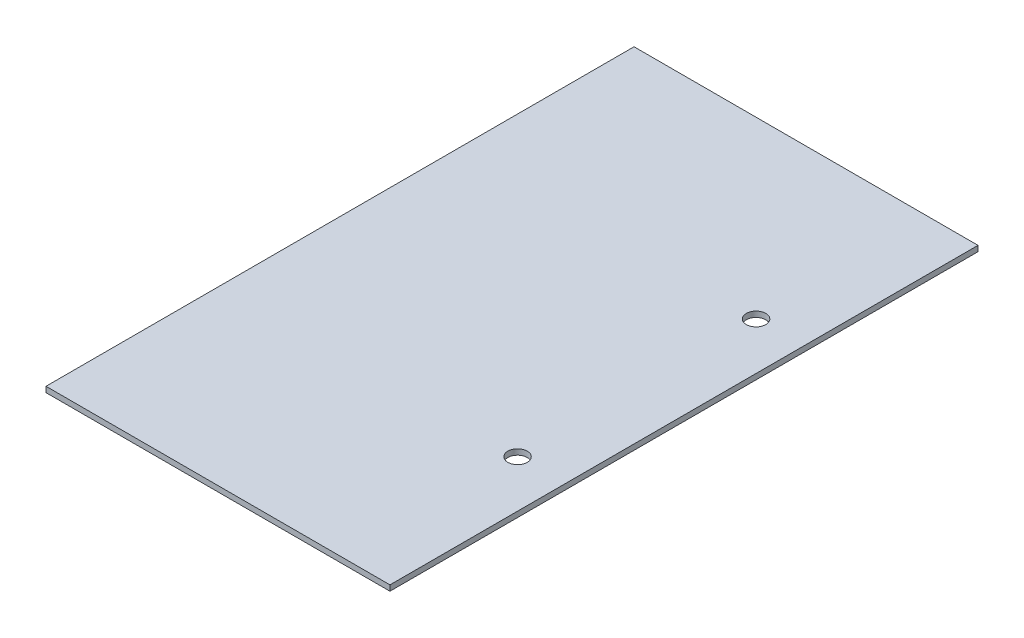
SolidWorks part; units mm, degrees
ref_plane "Front Plane" through (0, 0, 0) normal (0, 0, 1) x (1, 0, 0)
ref_plane "Top Plane" through (0, 0, 0) normal (0, 1, 0) x (1, 0, 0)
ref_plane "Right Plane" through (0, 0, 0) normal (1, 0, 0) x (0, 0, -1)
sketch "Sketch1" plane through (0, 0, 0) normal (0, 1, 0) x (1, 0, 0)
  line L0 (31, 0) -> (22.5, 0) construction
  line L1 (-31, 53) -> (31, 53)
  line L2 (-31, 53) -> (-31, -53)
  line L3 (-31, -53) -> (31, -53)
  line L4 (31, 53) -> (31, -53)
  line L5 (-31, 53) -> (31, -53) construction
  line L6 (-31, -53) -> (31, 53) construction
  line L7 (22.5, 0) -> (22.5, -21.5) construction
  circle A0 centre (22.5, -21.5) radius 1.75
  circle A1 centre (22.5, 21.5) radius 1.75
  point P0 (0, 0)
  dimension "D5" = 3.5
  dimension "D1" = 106
  dimension "D2" = 62
  dimension "D3" = 8.5
  dimension "D4" = 21.5
extrude "Boss-Extrude1" add sketch "Sketch1" along normal blind 1
sketch "Sketch2" plane through (0, 0, 0) normal (0, -1, 0) x (1, 0, 0)
  circle A0 centre (0, 0) radius 5
  dimension "D1" = 10
extrude "Boss-Extrude2" add sketch "Sketch2" along normal blind 17
fillet "Fillet1" radius 5 1 edges at (0, -17, -5)
